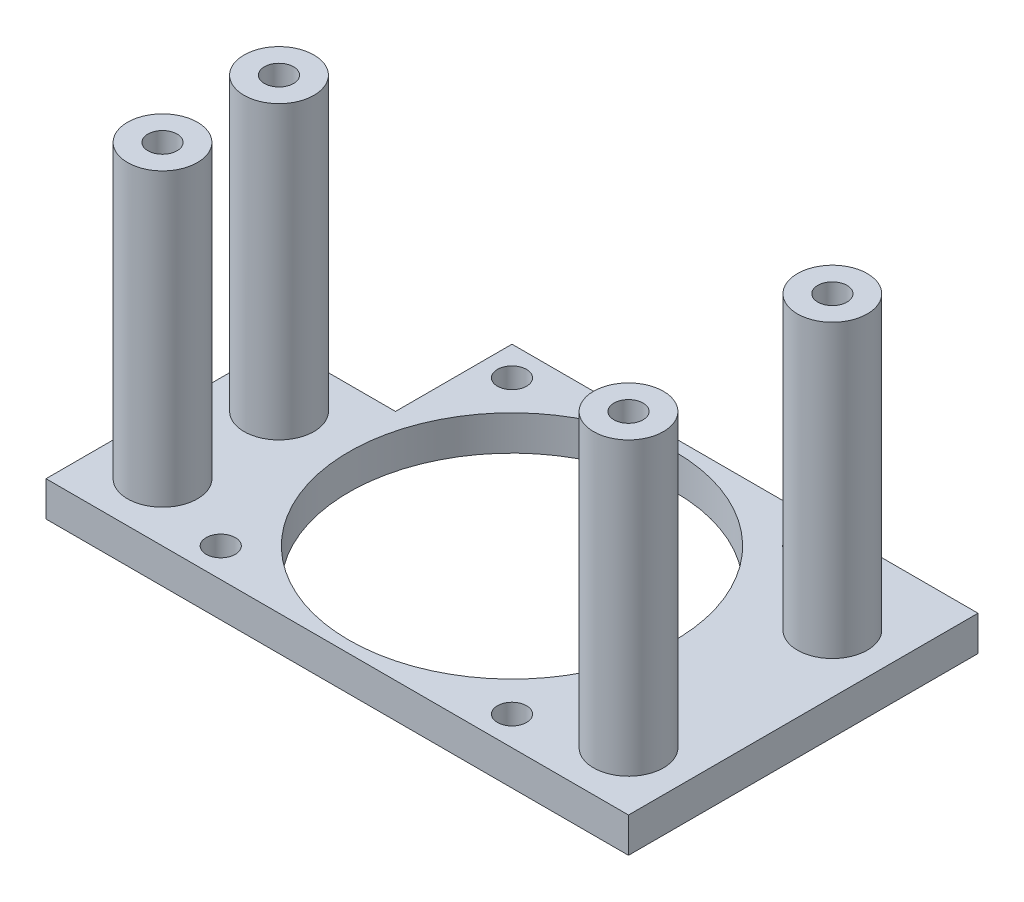
SolidWorks part; units mm, degrees
ref_plane "Front Plane" through (0, 0, 0) normal (0, 0, 1) x (1, 0, 0)
ref_plane "Top Plane" through (0, 0, 0) normal (0, 1, 0) x (1, 0, 0)
ref_plane "Right Plane" through (0, 0, 0) normal (1, 0, 0) x (0, 0, -1)
sketch "Sketch1" plane through (0, 0, 0) normal (0, 1, 0) x (1, 0, 0)
  line L0 (-53.7179, 25) -> (13.8462, 25) construction
  line L1 (-50, -30) -> (50, -30)
  line L2 (-30, 10) -> (-30, 30)
  line L3 (-30, 30) -> (50, 30)
  line L4 (-25, 31.9872) -> (-25, -36.859) construction
  line L5 (-47.9135, -25) -> (21.6297, -25) construction
  line L9 (-30, 10) -> (-50, 10)
  line L10 (-50, -30) -> (-50, 10)
  line L14 (50, 30) -> (50, -30)
  circle A0 centre (0, 0) radius 28
  circle A1 centre (-25, 25) radius 2.5
  circle A2 centre (25, 25) radius 2.5
  circle A3 centre (25, -25) radius 2.5
  circle A4 centre (-25, -25) radius 2.5
  point P0 (0, 0)
  point P20 (0, 0)
  point P25 (0, 0)
  point P26 (0, 0)
  dimension "D8" = 56
  dimension "D9" = 5
  dimension "D14" = 50
  dimension "D1" = 80
  dimension "D2" = 100
  dimension "D3" = 20
  dimension "D4" = 40
  dimension "D5" = 30
  dimension "D6" = 30
  dimension "D7" = 60
  dimension "D10" = 5
  dimension "D11" = 5
  dimension "D12" = 5
  dimension "D13" = 50
extrude "Boss-Extrude1" add sketch "Sketch1" along normal blind 6
sketch "Sketch2" plane through (0, 6, 0) normal (0, 1, 0) x (1, 0, 0)
  line L0 (-30, 30) -> (-30, 10) construction
  line L1 (-30, 10) -> (-50, 10) construction
  line L2 (-50, -30) -> (50, -30) construction
  line L3 (50, -30) -> (50, 30) construction
  line L4 (50, 30) -> (-30, 30) construction
  circle A0 centre (-40, 0) radius 6
  circle A1 centre (-40, -20) radius 6
  circle A2 centre (40, 15) radius 6
  circle A3 centre (40, -20) radius 6
  dimension "D1" = 10
  dimension "D2" = 12
  dimension "D3" = 12
  dimension "D5" = 10
  dimension "D6" = 10
  dimension "D7" = 12
  dimension "D8" = 12
  dimension "D9" = 10
  dimension "D10" = 10
  dimension "D11" = 10
  dimension "D12" = 15
  dimension "D4" = 10
extrude "Boss-Extrude2" add sketch "Sketch2" along normal blind 50
sketch "Sketch3" plane through (0, 56, 0) normal (0, 1, 0) x (1, 0, 0)
  circle A0 centre (-40, 0) radius 2.5
  circle A1 centre (-40, -20) radius 2.5
  circle A2 centre (40, -20) radius 2.5
  circle A3 centre (40, 15) radius 2.5
  dimension "D1" = 5
extrude "Cut-Extrude1" cut sketch "Sketch3" against normal through all
sketch "Sketch5" plane through (0, 0, 0) normal (0, -1, 0) x (1, 0, 0)
  circle A0 centre (-40, 0) radius 4.25
  circle A1 centre (-40, 20) radius 4.25
  circle A2 centre (40, 20) radius 4.25
  circle A3 centre (40, -15) radius 4.25
  dimension "D1" = 8.5
extrude "Cut-Extrude2" cut sketch "Sketch5" against normal blind 50
